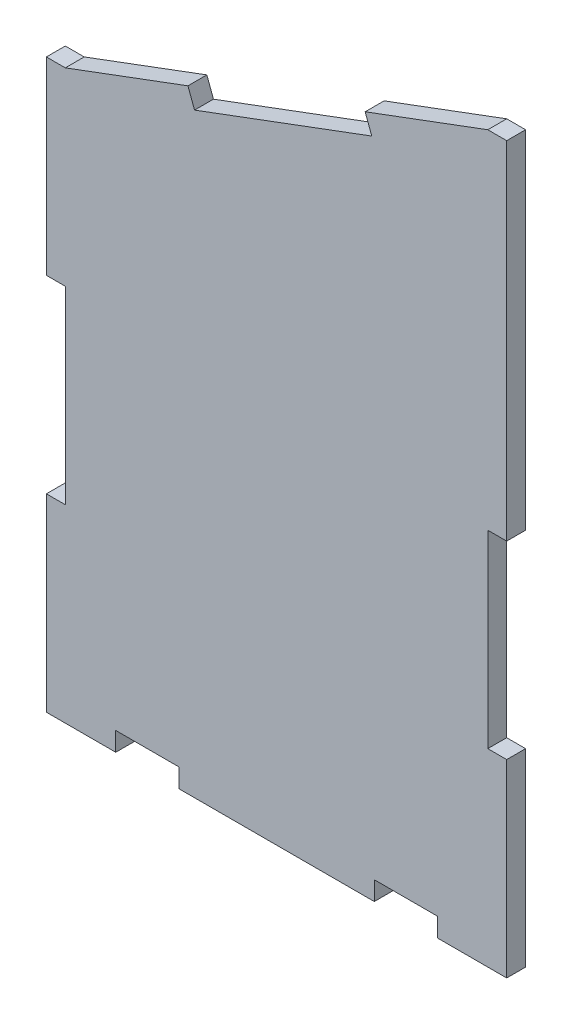
SolidWorks part; units mm, degrees
ref_plane "Front Plane" through (0, 0, 0) normal (0, 0, 1) x (1, 0, 0)
ref_plane "Top Plane" through (0, 0, 0) normal (0, 1, 0) x (1, 0, 0)
ref_plane "Right Plane" through (0, 0, 0) normal (1, 0, 0) x (0, 0, -1)
sketch "Model" plane through (0, 0, 0) normal (0, 0, 1) x (1, 0, 0)
  line L2 (292.8563, 164.9698) -> (292.8563, 134.9698) construction
  line L6 (292.8563, 249.9698) -> (292.8563, 194.9698)
  line L10 (292.8563, 134.9698) -> (219.8578, 134.9698) construction
  line L15 (289.8563, 194.9698) -> (292.8563, 194.9698)
  line L16 (292.8563, 249.9698) -> (289.8563, 249.9698)
  line L20 (289.8563, 164.9698) -> (292.8563, 164.9698)
  line L22 (292.8563, 134.9698) -> (281.8563, 134.9698)
  line L23 (281.8563, 134.9698) -> (281.8563, 137.9698)
  line L25 (289.8563, 194.9698) -> (289.8563, 164.9698)
  line L26 (292.8563, 246.8737) -> (292.1147, 247.0629) construction
  line L27 (292.8563, 249.9698) -> (292.1351, 247.0577) construction
  line L28 (290.9628, 247.1813) -> (289.8563, 249.9698) construction
  line L29 (219.8578, 134.9698) -> (219.8578, 164.9698)
  line L30 (281.8563, 137.9698) -> (271.8563, 137.9698)
  line L31 (219.8578, 164.9698) -> (222.8578, 164.9698)
  line L42 (222.8578, 164.9698) -> (222.8578, 194.9698)
  line L45 (222.8578, 194.9698) -> (219.8578, 194.9698)
  line L46 (219.8578, 194.9698) -> (219.8578, 224.9698)
  line L49 (219.8578, 224.9698) -> (222.8578, 224.9698)
  line L53 (222.8578, 224.9698) -> (242.3035, 232.2258)
  line L63 (271.8563, 137.9698) -> (271.8563, 134.9698)
  line L68 (271.8563, 134.9698) -> (240.8578, 134.9698)
  line L69 (256.357, 237.4698) -> (257.4058, 234.6591) construction
  line L70 (242.3035, 232.2258) -> (243.3523, 229.4151)
  line L71 (270.4105, 242.7137) -> (271.4593, 239.903)
  line L72 (271.4593, 239.903) -> (243.3523, 229.4151)
  line L73 (270.4105, 242.7137) -> (289.8563, 249.9698)
  line L74 (289.8563, 249.9698) -> (289.8563, 194.9698) construction
  line L77 (292.8563, 164.9698) -> (292.8563, 134.9698)
  line L78 (240.8578, 134.9698) -> (240.8578, 137.9698)
  line L79 (240.8578, 137.9698) -> (230.8578, 137.9698)
  line L80 (230.8578, 137.9698) -> (230.8578, 134.9698)
  line L81 (230.8578, 134.9698) -> (219.8578, 134.9698)
  point P2 (277.1663, 249.84)
  point P4 (414.3116, 222.6672)
  point P18 (291.3563, 179.9698)
  point P22 (179.0263, 224.9408)
  point P23 (279.0253, 249.9372)
  point P27 (290.9628, 250.114)
  point P29 (227.9628, 225.114)
  point P40 (390.8578, 224.9698)
  point P349 (396.8578, 224.9698)
  dimension "D3" = 11
  dimension "D4" = 10
  dimension "D5" = 30
  dimension "D6" = 3
  dimension "D7" = 30
  dimension "D8" = 30
  dimension "D9" = 3
  dimension "D10" = 10
  dimension "D11" = 3
  dimension "D12" = 55
  dimension "D13" = 30
  dimension "D14" = 11
  dimension "D15" = 30.9985
  dimension "D16" = 3
  dimension "D17" = 30
  dimension "D18" = 30
  dimension "D19" = 3
  dimension "D20" = 3
  dimension "D21" = 20.7554
  dimension "D22" = 20.7554
  dimension "D23" = 3
  dimension "D24" = 3
  dimension "D25" = 3
  dimension "D26" = 3
extrude "Boss-Extrude1" add sketch "Model" along normal blind 3
